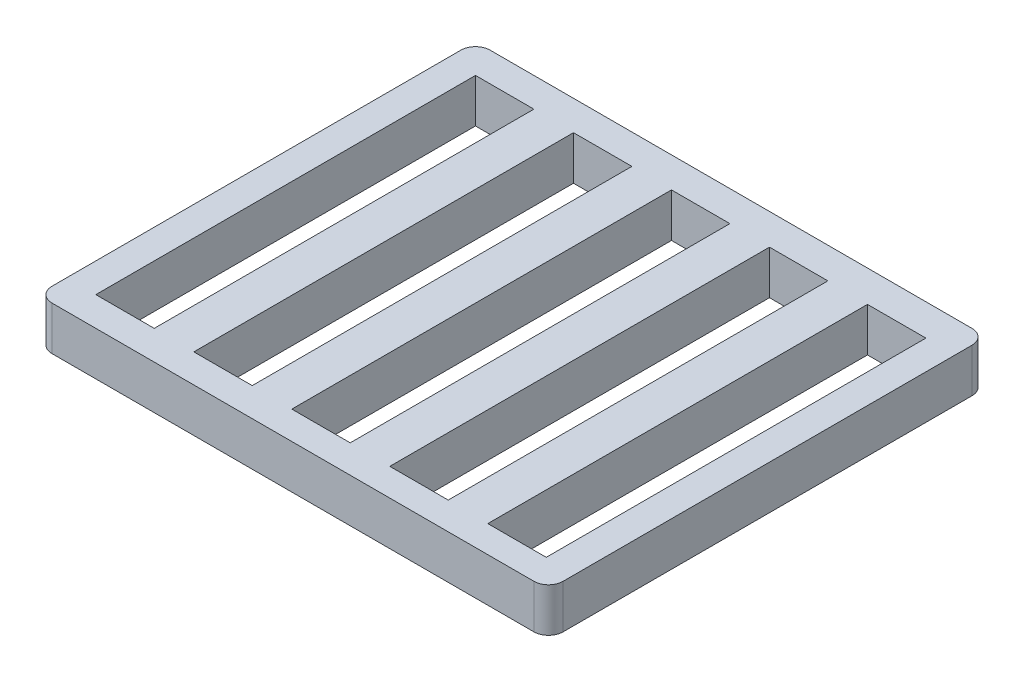
SolidWorks part; units mm, degrees
ref_plane "Front Plane" through (0, 0, 0) normal (0, 0, 1) x (1, 0, 0)
ref_plane "Top Plane" through (0, 0, 0) normal (0, 1, 0) x (1, 0, 0)
ref_plane "Right Plane" through (0, 0, 0) normal (1, 0, 0) x (0, 0, -1)
sketch "Sketch1" plane through (0, 0, 0) normal (0, 1, 0) x (1, 0, 0)
  line L0 (83.2175, -20) -> (83.2175, -280)
  line L5 (0, 0) -> (350, 0)
  line L6 (0, 0) -> (0, -300)
  line L7 (0, -300) -> (350, -300)
  line L8 (350, 0) -> (350, -300)
  line L9 (18.2175, -20) -> (58.2175, -20)
  line L10 (18.2175, -20) -> (18.2175, -280)
  line L11 (18.2175, -280) -> (58.2175, -280)
  line L12 (58.2175, -20) -> (58.2175, -280)
  line L13 (83.2175, -20) -> (123.2175, -20)
  line L14 (123.2175, -20) -> (123.2175, -280)
  line L15 (83.2175, -280) -> (123.2175, -280)
  line L16 (148.2175, -20) -> (148.2175, -280)
  line L17 (148.2175, -20) -> (188.2175, -20)
  line L18 (188.2175, -20) -> (188.2175, -280)
  line L19 (148.2175, -280) -> (188.2175, -280)
  line L20 (213.2175, -20) -> (213.2175, -280)
  line L21 (213.2175, -20) -> (253.2175, -20)
  line L22 (253.2175, -20) -> (253.2175, -280)
  line L23 (213.2175, -280) -> (253.2175, -280)
  line L24 (278.2175, -20) -> (278.2175, -280)
  line L25 (278.2175, -20) -> (318.2175, -20)
  line L26 (318.2175, -20) -> (318.2175, -280)
  line L27 (278.2175, -280) -> (318.2175, -280)
  line L28 (18.2175, -20) -> (83.2175, -20) construction
  dimension "D1" = 350
  dimension "D2" = 300
  dimension "D3" = 20
  dimension "D4" = 20
  dimension "D5" = 40
  dimension "D7" = 65
  dimension "D6" = 5
extrude "Boss-Extrude1" add sketch "Sketch1" along normal blind 30 contours L6 L5 L8 L7
sketch "Sketch3" plane through (0, 0, 0) normal (0, -1, 0) x (-1, 0, 0)
  line L0 (0, -300) -> (-350, -300) construction
  line L1 (-60, -20) -> (-20, -20)
  line L2 (-60, -20) -> (-60, -280)
  line L3 (-60, -280) -> (-20, -280)
  line L4 (-20, -20) -> (-20, -280)
  line L5 (0, 0) -> (-350, 0) construction
  line L6 (0, 0) -> (0, -300) construction
  line L7 (-127.5, -20.3913) -> (-127.5, -280.3913)
  line L8 (-127.5, -280.3913) -> (-87.5, -280.3913)
  line L9 (-87.5, -20.3913) -> (-87.5, -280.3913)
  line L10 (-127.5, -20.3913) -> (-87.5, -20.3913)
  line L11 (-195, -20.7826) -> (-195, -280.7826)
  line L12 (-195, -280.7826) -> (-155, -280.7826)
  line L13 (-155, -20.7826) -> (-155, -280.7826)
  line L14 (-195, -20.7826) -> (-155, -20.7826)
  line L15 (-262.5, -21.174) -> (-262.5, -281.174)
  line L16 (-262.5, -281.174) -> (-222.5, -281.174)
  line L17 (-222.5, -21.174) -> (-222.5, -281.174)
  line L18 (-262.5, -21.174) -> (-222.5, -21.174)
  line L19 (-330, -21.5653) -> (-330, -281.5653)
  line L20 (-330, -281.5653) -> (-290, -281.5653)
  line L21 (-290, -21.5653) -> (-290, -281.5653)
  line L22 (-330, -21.5653) -> (-290, -21.5653)
  line L23 (-60, -20) -> (-127.5, -20.3913) construction
  line L24 (-350, 0) -> (-350, -300) construction
  dimension "D1" = 20
  dimension "D2" = 20
  dimension "D3" = 20
  dimension "D4" = 40
  dimension "D8" = 20
  dimension "D5" = 5
extrude "Cut-Extrude1" cut sketch "Sketch3" against normal through all
fillet "Fillet1" radius 10 4 edges at (0, 15, 0) (0, 15, 300) (350, 15, 300) (350, 15, 0)
